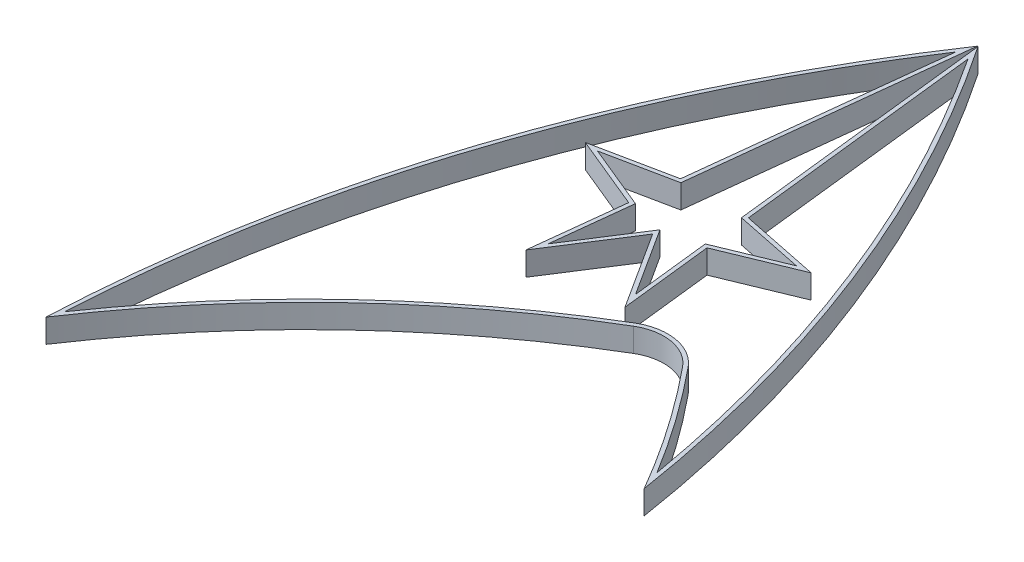
SolidWorks part; units mm, degrees
ref_plane "Front Plane" through (0, 0, 0) normal (0, 0, 1) x (1, 0, 0)
ref_plane "Top Plane" through (0, 0, 0) normal (0, 1, 0) x (1, 0, 0)
ref_plane "Right Plane" through (0, 0, 0) normal (1, 0, 0) x (0, 0, -1)
sketch "Sketch1" plane through (0, 0, 0) normal (0, 1, 0) x (1, 0, 0)
  line L10 (29.7241, 45.5525) -> (30.5369, 38.3256)
  line L11 (36.632, 48.4021) -> (29.7241, 45.5525)
  line L12 (29.1261, 50.8699) -> (35.6287, 49.5371)
  line L13 (26.9138, 70.5394) -> (29.1261, 50.8699)
  line L14 (21.5114, 50.8699) -> (23.7236, 70.5394)
  line L15 (15.0087, 49.5371) -> (21.5114, 50.8699)
  line L16 (20.9133, 45.5525) -> (14.0054, 48.4021)
  line L17 (19.7009, 34.7729) -> (20.9133, 45.5525)
  line L18 (25.3187, 43.524) -> (19.7009, 34.7729)
  line L19 (29.371, 37.2116) -> (25.3187, 43.524)
  line L29 (22.4239, 50.0361) -> (25.3187, 75.7743)
  line L30 (25.3187, 75.7743) -> (28.2135, 50.0361)
  line L31 (28.2135, 50.0361) -> (34.732, 48.7001)
  line L32 (34.732, 48.7001) -> (28.6462, 46.1896)
  line L33 (28.6462, 46.1896) -> (29.464, 38.9178)
  line L34 (29.464, 38.9178) -> (25.3187, 45.3751)
  line L35 (25.3187, 45.3751) -> (21.1734, 38.9178)
  line L36 (21.1734, 38.9178) -> (21.9913, 46.1896)
  line L37 (21.9913, 46.1896) -> (15.9054, 48.7001)
  line L39 (15.9054, 48.7001) -> (22.4239, 50.0361)
  arc A5 (47.6216, 20.4347) -> (38.3331, 34.0133) centre (-35, -26.1166) ccw
  arc A6 (38.3331, 34.0133) -> (32.5601, 35.0318) centre (34.8534, 31.16) ccw
  arc A7 (32.5601, 35.0318) -> (1.6083, 5.4751) centre (80.8889, -46.5628) ccw
  arc A8 (47.6216, 20.4347) -> (25.3187, 77.656) centre (-89.3626, 0) ccw
  arc A9 (25.3187, 77.656) -> (1.6083, 5.4751) centre (140, 0) ccw
  arc A23 (30.5369, 38.3256) -> (31.946, 37.5277) centre (31.5307, 38.4374) ccw
  arc A24 (42.6939, 32.5131) -> (40.2664, 35.5985) centre (-35, -26.1166) ccw
  arc A25 (40.2664, 35.5985) -> (31.946, 37.5277) centre (34.8534, 31.16) ccw
  arc A26 (42.6939, 32.5131) -> (37.9494, 47.8294) centre (-89.3626, 0) ccw
  arc A27 (37.9494, 47.8294) -> (36.632, 48.4021) centre (37.0133, 47.4777) ccw
  arc A28 (35.6287, 49.5371) -> (36.7569, 50.8909) centre (35.8295, 50.5167) ccw
  arc A29 (36.7569, 50.8909) -> (26.9138, 70.5394) centre (-89.3626, 0) ccw
  arc A30 (23.7236, 70.5394) -> (13.8806, 50.8909) centre (140, 0) ccw
  arc A31 (13.8806, 50.8909) -> (15.0087, 49.5371) centre (14.8079, 50.5167) ccw
  arc A32 (29.0619, 35.8249) -> (29.371, 37.2116) centre (28.5294, 36.6714) ccw
  arc A33 (29.0619, 35.8249) -> (4.727, 14.0437) centre (80.8889, -46.5628) ccw
  arc A34 (12.688, 47.8294) -> (4.727, 14.0437) centre (140, 0) ccw
  arc A35 (14.0054, 48.4021) -> (12.688, 47.8294) centre (13.6241, 47.4777) ccw
sketch "Sketch2" plane through (0, 0, 0) normal (0, 1, 0) x (1, 0, 0)
  line L10 (28.761, 50.5364) -> (25.9368, 75.6469)
  line L11 (36.775, 48.8938) -> (28.761, 50.5364)
  line L12 (29.2929, 45.8073) -> (36.775, 48.8938)
  line L13 (30.3475, 36.4309) -> (29.2929, 45.8073)
  line L14 (25.3187, 44.2645) -> (30.3475, 36.4309)
  line L15 (20.2899, 36.4309) -> (25.3187, 44.2645)
  line L16 (21.3445, 45.8073) -> (20.2899, 36.4309)
  line L17 (13.8624, 48.8938) -> (21.3445, 45.8073)
  line L18 (21.8764, 50.5364) -> (13.8624, 48.8938)
  line L19 (24.7006, 75.6469) -> (21.8764, 50.5364)
  line L20 (25.3187, 77.5637) -> (22.2414, 50.2029)
  line L21 (28.396, 50.2029) -> (25.3187, 77.5637)
  line L22 (35.413, 48.7647) -> (28.396, 50.2029)
  line L23 (28.8617, 46.0621) -> (35.413, 48.7647)
  line L24 (29.7585, 38.0888) -> (28.8617, 46.0621)
  line L25 (25.3187, 45.0049) -> (29.7585, 38.0888)
  line L26 (20.8789, 38.0888) -> (25.3187, 45.0049)
  line L27 (21.7757, 46.0621) -> (20.8789, 38.0888)
  line L28 (15.2244, 48.7647) -> (21.7757, 46.0621)
  line L29 (22.2414, 50.2029) -> (15.2244, 48.7647)
  line L30 (25.2829, 77.2456) -> (22.2414, 50.2029)
  line L31 (28.396, 50.2029) -> (25.3545, 77.2456)
  line L32 (35.413, 48.7647) -> (28.396, 50.2029)
  line L33 (28.8617, 46.0621) -> (35.413, 48.7647)
  line L34 (29.7585, 38.0888) -> (28.8617, 46.0621)
  line L35 (25.3187, 45.0049) -> (29.7585, 38.0888)
  line L36 (20.8789, 38.0888) -> (25.3187, 45.0049)
  line L37 (21.7757, 46.0621) -> (20.8789, 38.0888)
  line L38 (15.2244, 48.7647) -> (21.7757, 46.0621)
  line L39 (22.2414, 50.2029) -> (15.2244, 48.7647)
  arc A32 (24.7006, 75.6469) -> (2.3091, 7.592) centre (140, 0) ccw
  arc A33 (32.2543, 35.5481) -> (2.3091, 7.592) centre (80.8889, -46.5628) ccw
  arc A34 (38.7971, 34.3937) -> (32.2543, 35.5481) centre (34.8534, 31.16) ccw
  arc A35 (46.52, 23.5021) -> (38.7971, 34.3937) centre (-35, -26.1166) ccw
  arc A36 (46.52, 23.5021) -> (25.9368, 75.6469) centre (-89.3626, 0) ccw
  arc A37 (25.3187, 77.2987) -> (1.8384, 6.1852) centre (140, 0) ccw
  arc A38 (32.4582, 35.2039) -> (1.8384, 6.1852) centre (80.8889, -46.5628) ccw
  arc A39 (38.4878, 34.1401) -> (32.4582, 35.2039) centre (34.8534, 31.16) ccw
  arc A40 (47.2607, 21.4702) -> (25.3187, 77.2987) centre (-89.3626, 0) ccw
  arc A41 (47.2607, 21.4702) -> (38.4878, 34.1401) centre (-35, -26.1166) ccw
  arc A42 (25.2829, 77.2456) -> (1.8384, 6.1852) centre (140, 0) ccw
  arc A43 (32.4582, 35.2039) -> (1.8384, 6.1852) centre (80.8889, -46.5628) ccw
  arc A44 (38.4878, 34.1401) -> (32.4582, 35.2039) centre (34.8534, 31.16) ccw
  arc A45 (47.2607, 21.4702) -> (25.3545, 77.2456) centre (-89.3626, 0) ccw
  arc A46 (47.2607, 21.4702) -> (38.4878, 34.1401) centre (-35, -26.1166) ccw
  dimension "D1" = 0.2
  dimension "D2" = 0.2
  dimension "D3" = 0.4
extrude "Boss-Extrude1" add sketch "Sketch2" along normal blind 2.4
